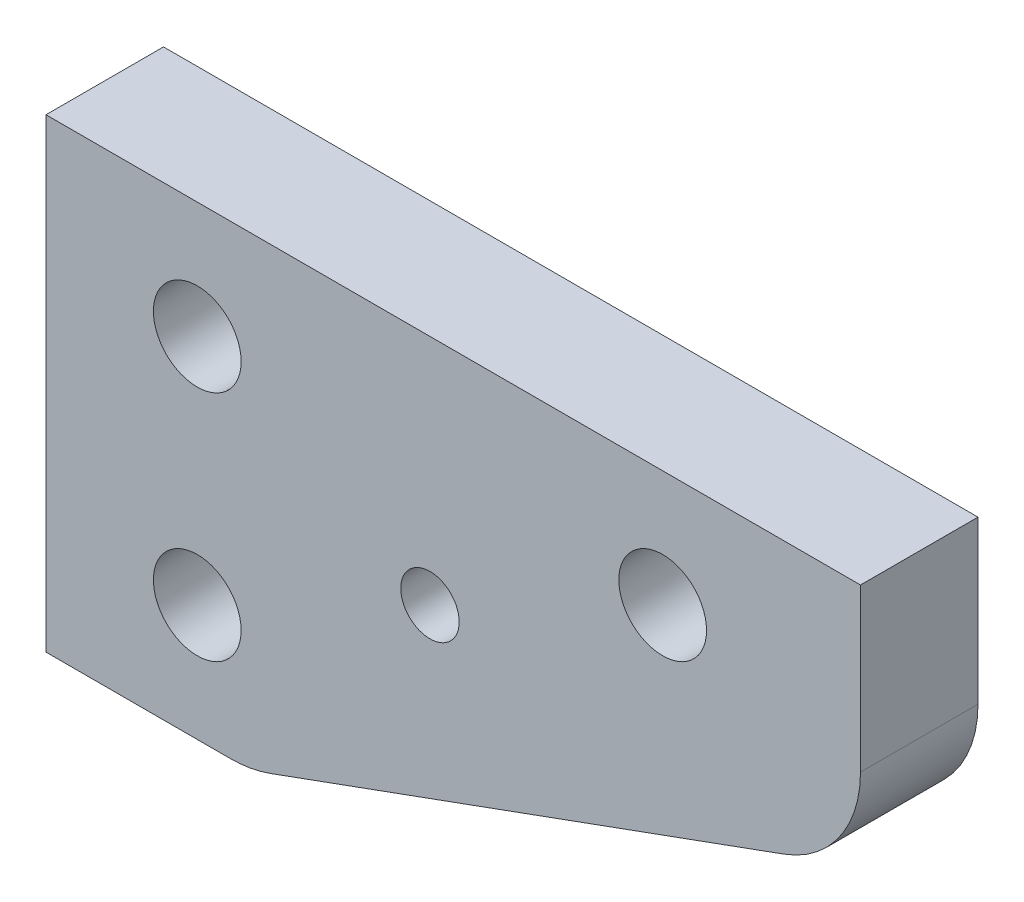
SolidWorks part; units mm, degrees
ref_plane "Front Plane" through (0, 0, 0) normal (0, 0, 1) x (1, 0, 0)
ref_plane "Top Plane" through (0, 0, 0) normal (0, 1, 0) x (1, 0, 0)
ref_plane "Right Plane" through (0, 0, 0) normal (1, 0, 0) x (0, 0, -1)
sketch "Sketch1" plane through (0, 0, 0) normal (0, 0, 1) x (1, 0, 0)
  line L0 (0, 0) -> (22.352, 0)
  line L1 (22.352, 0) -> (88.9, 24.2215)
  line L2 (88.9, 24.2215) -> (88.9, 50.8)
  line L3 (88.9, 50.8) -> (0, 50.8)
  line L4 (0, 50.8) -> (0, 0)
  circle A0 centre (16.51, 12.7) radius 4.7879
  circle A1 centre (16.51, 38.1) radius 4.7879
  circle A2 centre (67.31, 38.1) radius 4.7879
  circle A3 centre (41.91, 25.4) radius 3.1877
  point P14 (13.1799, 12.9192)
  point P15 (0, 0)
  point P16 (0, 0)
  dimension "D5" = 25.4
  dimension "D9" = 9.5758
  dimension "D12" = 6.3754
  dimension "D1" = 22.352
  dimension "D2" = 50.8
  dimension "D3" = 88.9
  dimension "D4" = 20
  dimension "D6" = 12.7
  dimension "D7" = 16.51
  dimension "D8" = 50.8
  dimension "D10" = 41.91
  dimension "D11" = 25.4
extrude "Boss-Extrude1" add sketch "Sketch1" along normal mid plane 12.827
fillet "Fillet1" radius 12.7 2 edges at (88.9, 24.2215, 0) (22.352, 0, 0)
